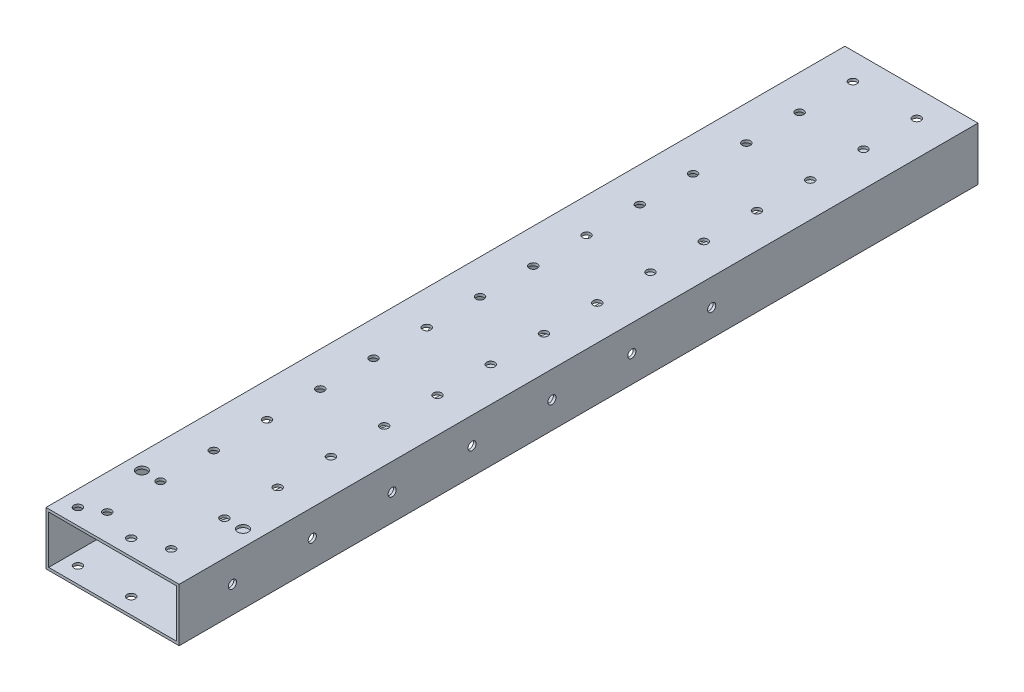
SolidWorks part; units mm, degrees
material "6063-T5"
ref_plane "前视基准面" through (0, 0, 0) normal (0, 0, 1) x (1, 0, 0)
ref_plane "上视基准面" through (0, 0, 0) normal (0, 1, 0) x (1, 0, 0)
ref_plane "右视基准面" through (0, 0, 0) normal (1, 0, 0) x (0, 0, -1)
sketch "草图1" plane through (0, 0, 0) normal (0, 0, 1) x (1, 0, 0)
  line L0 (-24, -9) -> (-24, 9)
  line L1 (-25, -10) -> (25, -10)
  line L2 (-25, -10) -> (-25, 10)
  line L3 (-25, 10) -> (25, 10)
  line L4 (25, -10) -> (25, 10)
  line L5 (0, 10) -> (0, -10) construction
  line L6 (-25, 0) -> (25, 0) construction
  line L7 (-24, 9) -> (24, 9)
  line L8 (24, -9) -> (24, 9)
  line L9 (-24, -9) -> (24, -9)
  point P0 (0, 0)
  dimension "D1" = 20
  dimension "D2" = 50
  dimension "D3" = 1
extrude "凸台-拉伸1" add sketch "草图1" along normal mid plane 300
sketch "草图2" plane through (0, 10, 0) normal (0, 1, 0) x (1, 0, 0)
  circle A0 centre (12, -140) radius 1.75 construction
  circle A1 centre (12, -140) radius 1.75 construction
  circle A2 centre (-12, -140) radius 1.75 construction
  circle A3 centre (-12, -140) radius 1.75 construction
  circle A4 centre (-12, -140) radius 1.525
  circle A5 centre (12, -140) radius 1.525
  dimension "D1" = 3.05
extrude "切除-拉伸1" cut sketch "草图2" against normal blind 10
pattern_linear "阵列(线性)1" count 15 spacing 20 along (0, 0, -1) of "切除-拉伸1"
sketch "草图3" plane through (25, 0, 0) normal (1, 0, 0) x (0, 0, -1)
  circle A0 centre (50, 0) radius 1.525 construction
  circle A1 centre (20, 0) radius 1.525 construction
  circle A2 centre (-10, 0) radius 1.525 construction
  circle A3 centre (-40, 0) radius 1.525 construction
  circle A4 centre (-70, 0) radius 1.525 construction
  circle A5 centre (-100, 0) radius 1.525 construction
  circle A6 centre (-130, 0) radius 1.525 construction
  circle A7 centre (50, 0) radius 1.525
  circle A8 centre (20, 0) radius 1.525
  circle A9 centre (-10, 0) radius 1.525
  circle A10 centre (-40, 0) radius 1.525
  circle A11 centre (-70, 0) radius 1.525
  circle A12 centre (-100, 0) radius 1.525
  circle A13 centre (-130, 0) radius 1.525
extrude "切除-拉伸2" cut sketch "草图3" against normal blind 100
sketch "草图4" plane through (0, -10, 0) normal (0, -1, 0) x (1, 0, 0)
  circle A0 centre (1, 144) radius 1.25 construction
  circle A1 centre (-19, 144) radius 1.25 construction
  circle A2 centre (1, 144) radius 1.25 construction
  circle A3 centre (-19, 144) radius 1.25 construction
  circle A4 centre (-19, 144) radius 1.525
  circle A5 centre (1, 144) radius 1.525
  dimension "D1" = 3.05
extrude "切除-拉伸3" cut sketch "草图4" against normal blind 100
sketch "草图5" plane through (0, -10, 0) normal (0, -1, 0) x (1, 0, 0)
  line L0 (232, 110) -> (-272, 110) construction
  line L1 (232, 130) -> (-272, 130) construction
  line L2 (25, 110) -> (-25, 110) construction
  line L3 (25, 130) -> (-25, 130) construction
  line L4 (-25, 150) -> (-25, -150) construction
  line L5 (25, 150) -> (25, -150) construction
  line L6 (-25, 130) -> (25, 110) construction
  line L7 (-19, 120) -> (19, 120) construction
  circle A0 centre (19, 120) radius 2.025
  circle A1 centre (-19, 120) radius 2.025
  point P14 (0, 120)
  dimension "D2" = 4.05
  dimension "D1" = 6
extrude "切除-拉伸4" cut sketch "草图5" against normal blind 39
sketch "草图6" plane through (0, -9, 0) normal (0, 1, 0) x (1, 0, 0)
  line L0 (-12, 100) -> (-12, 80) construction
  line L1 (-6.5, 100) -> (-6.5, 80)
  line L2 (-17.5, 100) -> (-17.5, 80)
  line L3 (0, 0) -> (0, 184.9769) construction
  line L4 (12, 100) -> (12, 80) construction
  line L5 (6.5, 100) -> (6.5, 80)
  line L6 (17.5, 100) -> (17.5, 80)
  arc A0 (-6.5, 100) -> (-17.5, 100) centre (-12, 100) ccw
  arc A1 (-17.5, 80) -> (-6.5, 80) centre (-12, 80) ccw
  arc A2 (6.5, 100) -> (17.5, 100) centre (12, 100) cw
  arc A3 (17.5, 80) -> (6.5, 80) centre (12, 80) cw
  point P4 (-12, 90)
  point P14 (12, 90)
  dimension "D1" = 5.5
sketch "草图7" plane through (0, -9, 0) normal (0, 1, 0) x (1, 0, 0)
  circle A0 centre (-12, -100) radius 5.5
  circle A1 centre (12, -100) radius 5.5
  dimension "D1" = 11
extrude "切除-拉伸6" cut sketch "草图7" against normal blind 10
extrude "切除-拉伸7" cut sketch "草图6" against normal blind 10
pattern_linear "阵列(线性)2" count 4 spacing 60 along (0, 0, 1) of "切除-拉伸7"
sketch "草图9" plane through (-25, 0, 0) normal (-1, 0, 0) x (0, 0, 1)
  circle A0 centre (-50, 0) radius 5.5
  dimension "D1" = 11
extrude "切除-拉伸8" cut sketch "草图9" against normal blind 10
pattern_linear "阵列(线性)3" count 6 spacing 30 along (0, 0, 1) of "切除-拉伸8"
sketch "草图10" plane through (0, -10, 0) normal (0, -1, 0) x (1, 0, 0)
  circle A0 centre (19, -140) radius 2.025 construction
  circle A1 centre (-19, -140) radius 2.025 construction
  circle A2 centre (19, -140) radius 2.025
  circle A3 centre (-19, -140) radius 2.025
extrude "切除-拉伸9" cut sketch "草图10" against normal blind 10
sketch "草图11" plane through (0, -10, 0) normal (0, -1, 0) x (1, 0, 0)
  line L0 (19, -140) -> (19, -122) construction
  line L1 (19, -122) -> (-19, -122) construction
  line L2 (-19, -122) -> (-19, -140) construction
  circle A0 centre (-19, -122) radius 2.025
  circle A1 centre (19, -122) radius 2.025
  dimension "D1" = 4.05
  dimension "D2" = 18
extrude "切除-拉伸10" cut sketch "草图11" against normal blind 8
